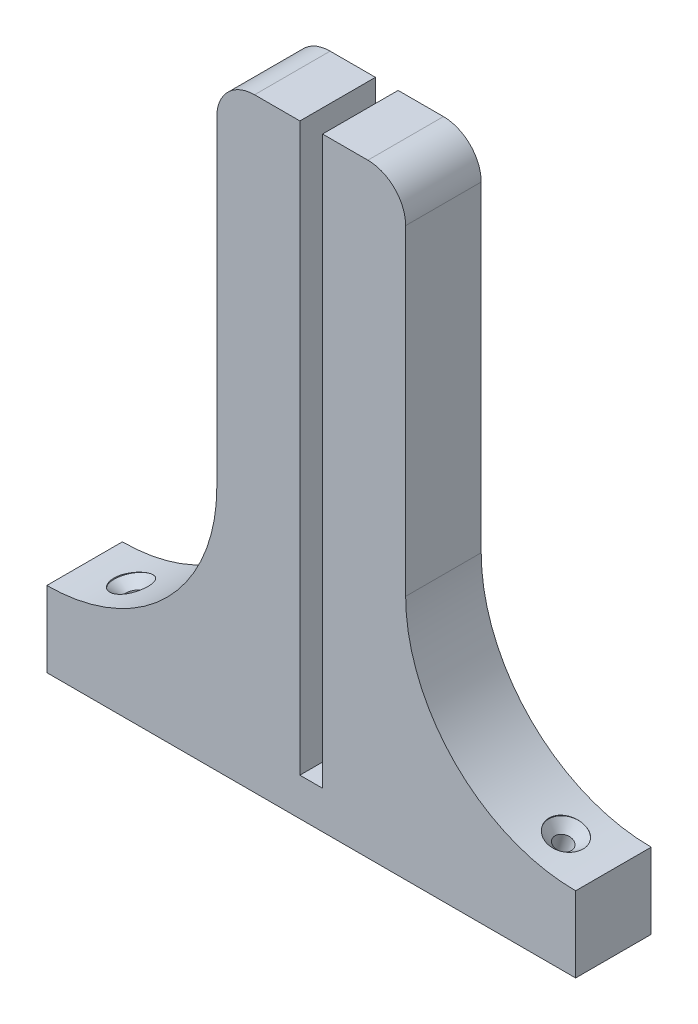
SolidWorks part; units mm, degrees
ref_plane "Plan de face" through (0, 0, 0) normal (0, 0, 1) x (1, 0, 0)
ref_plane "Plan de dessus" through (0, 0, 0) normal (0, 1, 0) x (1, 0, 0)
ref_plane "Plan de droite" through (0, 0, 0) normal (1, 0, 0) x (0, 0, -1)
sketch "Esquisse1" plane through (0, 0, 0) normal (0, 0, 1) x (1, 0, 0)
  line L0 (-70, 0) -> (70, 0)
  line L1 (70, 0) -> (70, 20)
  line L2 (25, 65) -> (25, 160)
  line L3 (25, 160) -> (-25, 160)
  line L4 (0, -36.4078) -> (0, 122.8519) construction
  line L5 (-70, 0) -> (-70, 20)
  line L6 (-25, 65) -> (-25, 160)
  arc A0 (70, 20) -> (25, 65) centre (70, 65) cw
  arc A1 (-70, 20) -> (-25, 65) centre (-70, 65) ccw
  point P4 (0, 0)
  point P15 (0, 160)
  dimension "D1" = 140
  dimension "D2" = 20
  dimension "D3" = 50
  dimension "D4" = 160
extrude "Boss.-Extru.1" add sketch "Esquisse1" along normal blind 20
fillet "Congé1" radius 10 2 edges at (-25, 160, 10) (25, 160, 10)
sketch "Esquisse2" plane through (0, 0, 20) normal (0, 0, 1) x (1, 0, 0)
  line L0 (-3, 10) -> (-3, 160)
  line L1 (-3, 10) -> (3, 10)
  line L2 (-3, 160) -> (3, 160)
  line L3 (3, 10) -> (3, 160)
  line L4 (-3, 10) -> (3, 160) construction
  line L5 (-3, 160) -> (3, 10) construction
  line L6 (-70, 0) -> (70, 0) construction
  line L7 (15, 160) -> (-15, 160) construction
  point P1 (0, 85)
  point P2 (0, 10)
  dimension "D1" = 6
  dimension "D2" = 10
extrude "Enlèv. mat.-Extru.1" cut sketch "Esquisse2" against normal blind 20
sketch "Esquisse3" plane through (-25, 0, 0) normal (-1, 0, 0) x (0, 0, 1)
  line L0 (10, 150) -> (10, 65) construction
  line L1 (20, 150) -> (0, 150) construction
  line L2 (20, 65) -> (0, 65) construction
  text T0 "Aïe Lab" font "Calibri" height in points 22
extrude "Enlèv. mat.-Extru.2" cut sketch "Esquisse3" against normal blind 0.6
hole_wizard "Fraisage pour vis à tête fraisée M41" positions "Esquisse3D1" profile "Esquisse5" countersink size "M4" standard "Ansi Metric" end condition through all
sketch3d "Esquisse3D1"
  point P0 (57.5305, 21.7622, 10.1298)
sketch "Esquisse5" plane through (57.5305, 21.7622, 10.1298) normal (0, 0, 1) x (-0.9608, 0.2771, 0)
  line L0 (0, 0) -> (0, 56.2488)
  line L1 (0, 56.2488) -> (2.25, 56.2488)
  line L2 (2.25, 56.2488) -> (2.25, 2.45)
  line L3 (2.25, 2.45) -> (4.7, 0)
  line L5 (4.7, 0) -> (0, 0)
  line L6 (-2.25, 2.45) -> (-4.7, 0) construction
  line L11 (0, -6.35) -> (0, 107.95) construction
  dimension "Diamètre du perçage jusqu'au prochain" = 4.5
  dimension "Profondeur du perçage jusqu'au prochain" = 56.2488
  dimension "Diamètre du fraisage entrant" = 9.4
  dimension "Angle du fraisage entrant" = 90
mirror "Symétrie1" about plane through (0, 0, 0) normal (1, 0, 0) of "Fraisage pour vis à tête fraisée M41"
